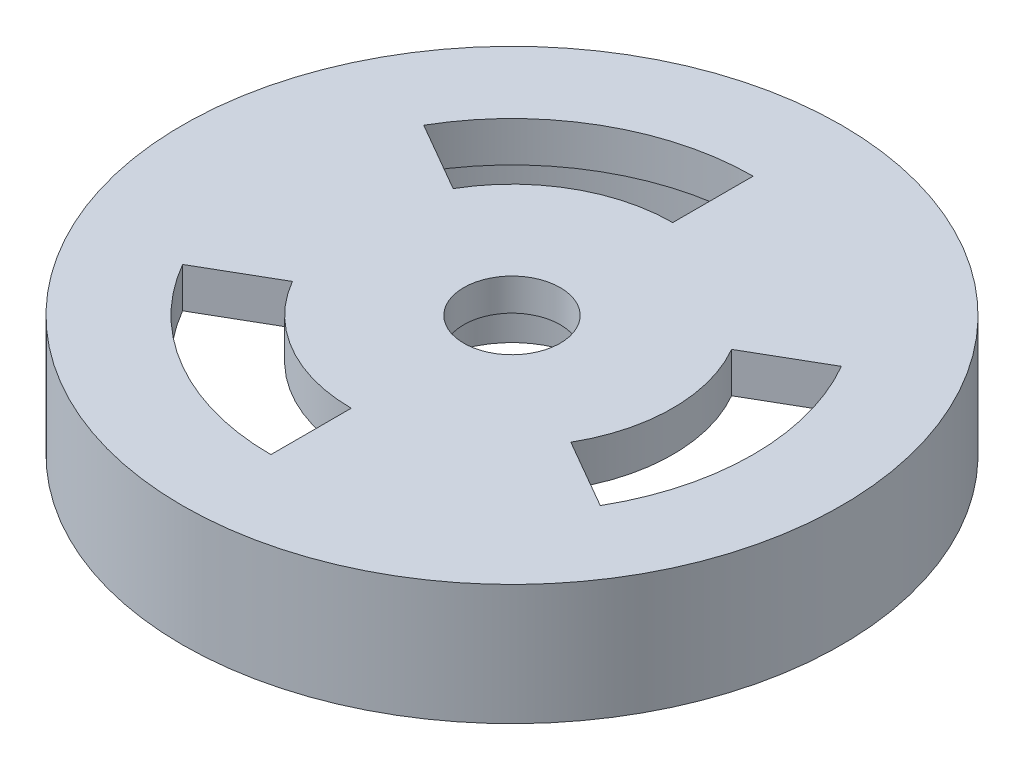
SolidWorks part; units mm, degrees
ref_plane "前视基准面" through (0, 0, 0) normal (0, 0, 1) x (1, 0, 0)
ref_plane "上视基准面" through (0, 0, 0) normal (0, 1, 0) x (1, 0, 0)
ref_plane "右视基准面" through (0, 0, 0) normal (1, 0, 0) x (0, 0, -1)
sketch "Sketch1" plane through (0, 0, 0) normal (0, 1, 0) x (1, 0, 0)
  circle A0 centre (0, 0) radius 38
  circle A1 centre (0, 0) radius 41
  dimension "D1" = 76
  dimension "D2" = 3
extrude "Boss-Extrude1" add sketch "Sketch1" along normal blind 10
sketch "Sketch3" plane through (0, 10, 0) normal (0, 1, 0) x (1, 0, 0)
  circle A0 centre (0, 0) radius 41
extrude "Boss-Extrude2" add sketch "Sketch3" along normal blind 5
sketch "Sketch4" plane through (0, 10, 0) normal (0, -1, 0) x (1, 0, 0)
  circle A0 centre (0, 0) radius 12.5
  dimension "D1" = 25
extrude "Boss-Extrude3" add sketch "Sketch4" along normal blind 5
sketch "Sketch5" plane through (0, 5, 0) normal (0, -1, 0) x (1, 0, 0)
  circle A0 centre (0, 0) radius 10
  dimension "D1" = 20
extrude "Cut-Extrude1" cut sketch "Sketch5" against normal blind 6
sketch "Sketch6" plane through (0, 11, 0) normal (0, -1, 0) x (1, 0, 0)
  circle A0 centre (0, 0) radius 6
  dimension "D1" = 12
extrude "Cut-Extrude2" cut sketch "Sketch6" against normal through all
sketch "Sketch7" plane through (0, 10, 0) normal (0, -1, 0) x (1, 0, 0)
  line L0 (0, 20) -> (0, 30)
  line L1 (-25.9808, 15) -> (-17.3205, 10)
  line L2 (17.3205, -10) -> (25.9808, -15)
  line L3 (25.9808, 15) -> (17.3205, 10)
  line L4 (-17.3205, -10) -> (-25.9808, -15)
  line L5 (0, -30) -> (0, -20)
  arc A0 (0, 30) -> (-25.9808, 15) centre (0, 0) ccw
  arc A1 (0, 20) -> (-17.3205, 10) centre (0, 0) ccw
  arc A2 (25.9808, -15) -> (25.9808, 15) centre (0, 0) ccw
  arc A3 (17.3205, -10) -> (17.3205, 10) centre (0, 0) ccw
  arc A4 (-25.9808, -15) -> (0, -30) centre (0, 0) ccw
  arc A5 (-17.3205, -10) -> (0, -20) centre (0, 0) ccw
  point P16 (0, 0)
  dimension "D1" = 10
  dimension "D2" = 20
  dimension "D3" = 60
  dimension "D4" = 3
extrude "Cut-Extrude3" cut sketch "Sketch7" against normal through all
